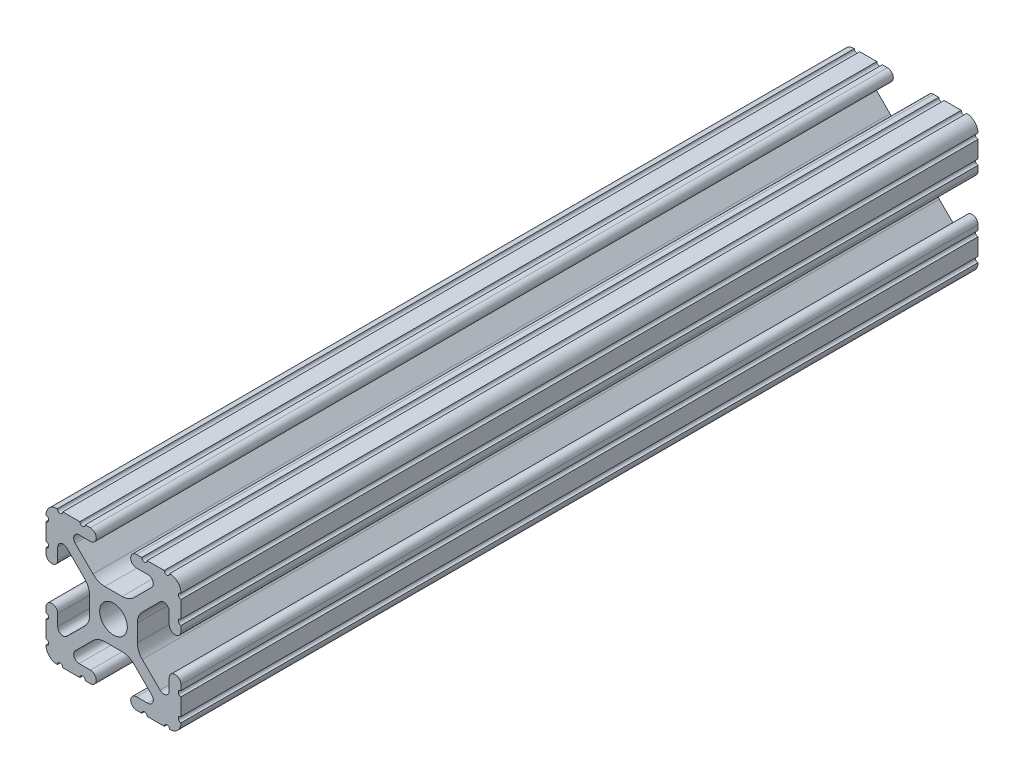
SolidWorks part; units mm, degrees
ref_plane "Front Plane" through (0, 0, 0) normal (0, 0, 1) x (1, 0, 0)
ref_plane "Top Plane" through (0, 0, 0) normal (0, 1, 0) x (1, 0, 0)
ref_plane "Right Plane" through (0, 0, 0) normal (1, 0, 0) x (0, 0, -1)
ref_plane "Plane1" through (0, 0, -381) normal (0, 0, -1) x (-1, 0, 0)
sketch "Sketch1" plane through (0, 0, -381) normal (0, 0, -1) x (-1, 0, 0)
  line L0 (12.7, -9.5504) -> (12.7, -6.3331)
  line L1 (12.7, -5.3171) -> (12.7, -4.3434)
  line L2 (10.4902, -4.3434) -> (10.4902, -6.4748)
  line L3 (8.7558, -7.1932) -> (5.4257, -3.8632)
  line L4 (4.4958, -1.6181) -> (4.4958, 1.6181)
  line L5 (5.4257, 3.8632) -> (8.7558, 7.1932)
  line L6 (10.4902, 6.4748) -> (10.4902, 4.3434)
  line L7 (12.7, 4.3434) -> (12.7, 5.3171)
  line L8 (12.7, 6.3331) -> (12.7, 9.5504)
  line L9 (9.5504, 12.7) -> (6.3331, 12.7)
  line L10 (5.3171, 12.7) -> (4.3434, 12.7)
  line L11 (4.3434, 10.4902) -> (6.4748, 10.4902)
  line L12 (7.1932, 8.7558) -> (3.8632, 5.4257)
  line L13 (1.6181, 4.4958) -> (-1.6181, 4.4958)
  line L14 (-3.8632, 5.4257) -> (-7.1932, 8.7558)
  line L15 (-6.4748, 10.4902) -> (-4.3434, 10.4902)
  line L16 (-4.3434, 12.7) -> (-5.3171, 12.7)
  line L17 (-6.3331, 12.7) -> (-9.5504, 12.7)
  line L18 (-12.7, 9.5504) -> (-12.7, 6.3331)
  line L19 (-12.7, 5.3171) -> (-12.7, 4.3434)
  line L20 (-10.4902, 4.3434) -> (-10.4902, 6.4748)
  line L21 (-8.7558, 7.1932) -> (-5.4257, 3.8632)
  line L22 (-4.4958, 1.6181) -> (-4.4958, -1.6181)
  line L23 (-5.4257, -3.8632) -> (-8.7558, -7.1932)
  line L24 (-10.4902, -6.4748) -> (-10.4902, -4.3434)
  line L25 (-12.7, -4.3434) -> (-12.7, -5.3171)
  line L26 (-12.7, -6.3331) -> (-12.7, -9.5504)
  line L27 (-9.5504, -12.7) -> (-6.3331, -12.7)
  line L28 (-5.3171, -12.7) -> (-4.3434, -12.7)
  line L29 (-4.3434, -10.4902) -> (-6.4748, -10.4902)
  line L30 (-7.1932, -8.7558) -> (-3.8632, -5.4257)
  line L31 (-1.6181, -4.4958) -> (1.6181, -4.4958)
  line L32 (3.8632, -5.4257) -> (7.1932, -8.7558)
  line L33 (6.4748, -10.4902) -> (4.3434, -10.4902)
  line L34 (4.3434, -12.7) -> (5.3171, -12.7)
  line L35 (6.3331, -12.7) -> (9.5504, -12.7)
  arc A0 (12.6998, -10.5664) -> (12.7, -9.5504) centre (12.7, -10.0584) cw
  arc A1 (12.7, -6.3331) -> (12.7, -5.3171) centre (12.7, -5.8251) cw
  arc A2 (12.7, -4.3434) -> (10.4902, -4.3434) centre (11.5951, -4.3434) ccw
  arc A3 (10.4902, -6.4748) -> (8.7558, -7.1932) centre (9.4742, -6.4748) cw
  arc A4 (5.4257, -3.8632) -> (4.4958, -1.6181) centre (7.6708, -1.6181) cw
  arc A5 (4.4958, 1.6181) -> (5.4257, 3.8632) centre (7.6708, 1.6181) cw
  arc A6 (8.7558, 7.1932) -> (10.4902, 6.4748) centre (9.4742, 6.4748) cw
  arc A7 (10.4902, 4.3434) -> (12.7, 4.3434) centre (11.5951, 4.3434) ccw
  arc A8 (12.7, 5.3171) -> (12.7, 6.3331) centre (12.7, 5.8251) cw
  arc A9 (12.7, 9.5504) -> (12.6998, 10.5664) centre (12.7, 10.0584) cw
  arc A10 (12.6998, 10.5664) -> (10.5664, 12.6998) centre (10.5918, 10.5918) ccw
  arc A11 (10.5664, 12.6998) -> (9.5504, 12.7) centre (10.0584, 12.7) cw
  arc A12 (6.3331, 12.7) -> (5.3171, 12.7) centre (5.8251, 12.7) cw
  arc A13 (4.3434, 12.7) -> (4.3434, 10.4902) centre (4.3434, 11.5951) ccw
  arc A14 (6.4748, 10.4902) -> (7.1932, 8.7558) centre (6.4748, 9.4742) cw
  arc A15 (3.8632, 5.4257) -> (1.6181, 4.4958) centre (1.6181, 7.6708) cw
  arc A16 (-1.6181, 4.4958) -> (-3.8632, 5.4257) centre (-1.6181, 7.6708) cw
  arc A17 (-7.1932, 8.7558) -> (-6.4748, 10.4902) centre (-6.4748, 9.4742) cw
  arc A18 (-4.3434, 10.4902) -> (-4.3434, 12.7) centre (-4.3434, 11.5951) ccw
  arc A19 (-5.3171, 12.7) -> (-6.3331, 12.7) centre (-5.8251, 12.7) cw
  arc A20 (-9.5504, 12.7) -> (-10.5664, 12.6998) centre (-10.0584, 12.7) cw
  arc A21 (-10.5664, 12.6998) -> (-12.6998, 10.5664) centre (-10.5918, 10.5918) ccw
  arc A22 (-12.6998, 10.5664) -> (-12.7, 9.5504) centre (-12.7, 10.0584) cw
  arc A23 (-12.7, 6.3331) -> (-12.7, 5.3171) centre (-12.7, 5.8251) cw
  arc A24 (-12.7, 4.3434) -> (-10.4902, 4.3434) centre (-11.5951, 4.3434) ccw
  arc A25 (-10.4902, 6.4748) -> (-8.7558, 7.1932) centre (-9.4742, 6.4748) cw
  arc A26 (-5.4257, 3.8632) -> (-4.4958, 1.6181) centre (-7.6708, 1.6181) cw
  arc A27 (-4.4958, -1.6181) -> (-5.4257, -3.8632) centre (-7.6708, -1.6181) cw
  arc A28 (-8.7558, -7.1932) -> (-10.4902, -6.4748) centre (-9.4742, -6.4748) cw
  arc A29 (-10.4902, -4.3434) -> (-12.7, -4.3434) centre (-11.5951, -4.3434) ccw
  arc A30 (-12.7, -5.3171) -> (-12.7, -6.3331) centre (-12.7, -5.8251) cw
  arc A31 (-12.7, -9.5504) -> (-12.6998, -10.5664) centre (-12.7, -10.0584) cw
  arc A32 (-12.6998, -10.5664) -> (-10.5664, -12.6998) centre (-10.5918, -10.5918) ccw
  arc A33 (-10.5664, -12.6998) -> (-9.5504, -12.7) centre (-10.0584, -12.7) cw
  arc A34 (-6.3331, -12.7) -> (-5.3171, -12.7) centre (-5.8251, -12.7) cw
  arc A35 (-4.3434, -12.7) -> (-4.3434, -10.4902) centre (-4.3434, -11.5951) ccw
  arc A36 (-6.4748, -10.4902) -> (-7.1932, -8.7558) centre (-6.4748, -9.4742) cw
  arc A37 (-3.8632, -5.4257) -> (-1.6181, -4.4958) centre (-1.6181, -7.6708) cw
  arc A38 (1.6181, -4.4958) -> (3.8632, -5.4257) centre (1.6181, -7.6708) cw
  arc A39 (7.1932, -8.7558) -> (6.4748, -10.4902) centre (6.4748, -9.4742) cw
  arc A40 (4.3434, -10.4902) -> (4.3434, -12.7) centre (4.3434, -11.5951) ccw
  arc A41 (5.3171, -12.7) -> (6.3331, -12.7) centre (5.8251, -12.7) cw
  arc A42 (9.5504, -12.7) -> (10.5664, -12.6998) centre (10.0584, -12.7) cw
  arc A43 (10.5664, -12.6998) -> (12.6998, -10.5664) centre (10.5918, -10.5918) ccw
  circle A44 centre (0, 0) radius 2.6035
extrude "Boss-Extrude1" add sketch "Sketch1" against normal blind 150
